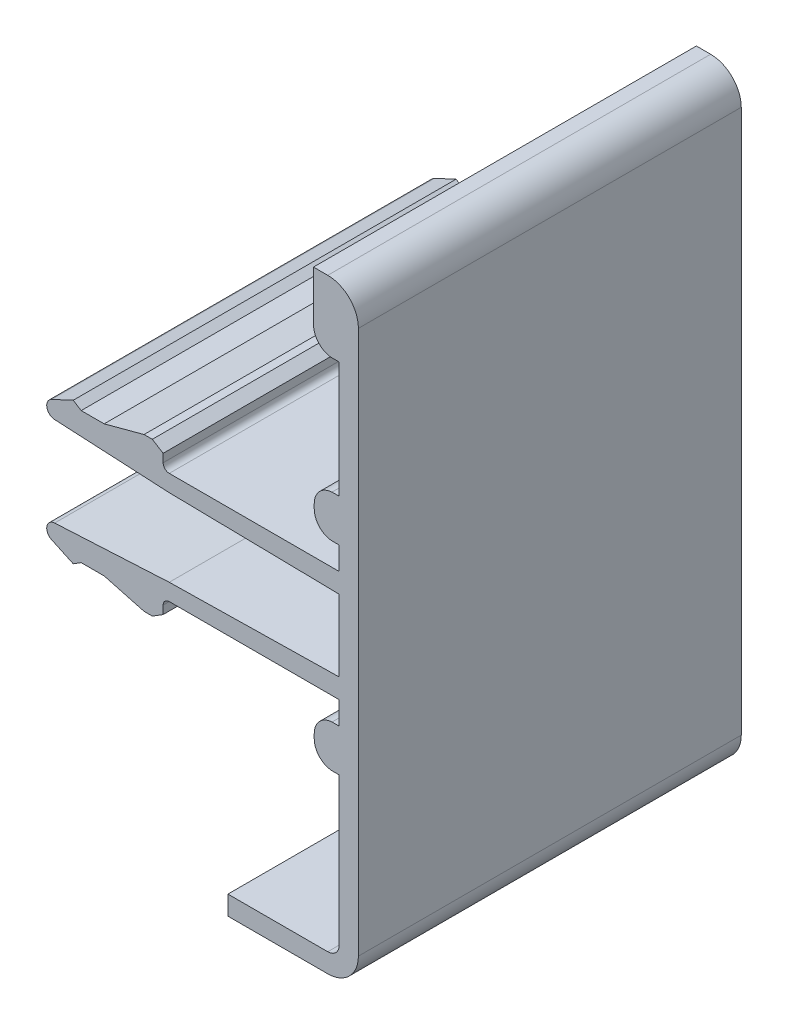
SolidWorks part; units mm, degrees
material "6005-T5"
ref_plane "Front" through (0, 0, 0) normal (0, 0, 1) x (1, 0, 0)
ref_plane "Top" through (0, 0, 0) normal (0, 1, 0) x (1, 0, 0)
ref_plane "Right" through (0, 0, 0) normal (1, 0, 0) x (0, 0, -1)
sketch "Sk Main Extrusion" plane through (0, 0, 0) normal (0, 0, 1) x (1, 0, 0)
  line L0 (-3.83, 2.5328) -> (-11.3125, 2.9251)
  line L5 (-3.83, -2.5328) -> (-11.3125, -2.9251)
  line L6 (6.7989, -5.1201) -> (7.27, -5.1201)
  line L7 (6.7989, -7.8799) -> (7.27, -7.8799)
  line L8 (6.7989, 7.8799) -> (7.27, 7.8799)
  line L9 (6.7989, 5.1201) -> (7.27, 5.1201)
  line L10 (7.27, -7.8799) -> (7.27, -17.5)
  line L11 (6.7981, 15.47) -> (7.27, 15.47)
  line L12 (0, -18.25) -> (0, -19.5)
  line L13 (5.638, 6.65) -> (5.638, 6.35)
  line L14 (7.27, 5.1201) -> (7.27, 3.625)
  line L15 (7.27, 3.625) -> (-3.83, 3.625)
  line L16 (-4.23, 4.025) -> (-4.23, 4.56)
  line L17 (-4.23, 4.56) -> (-4.9341, 5)
  line L18 (-4.9341, 5) -> (-5.4741, 5)
  line L19 (-5.4741, 5) -> (-8.08, 4.3)
  line L20 (-8.08, 4.3) -> (-9.58, 4.3)
  line L21 (-9.58, 4.3) -> (-10.1001, 4.625)
  line L22 (-10.1001, 4.625) -> (-11.5147, 3.9654)
  line L23 (-3.83, 2.5328) -> (7.27, 2.339)
  line L24 (7.27, 2.339) -> (7.27, -2.339)
  line L25 (7.27, -2.339) -> (-3.83, -2.5328)
  line L26 (-11.5147, -3.9654) -> (-10.1001, -4.625)
  line L27 (-10.1001, -4.625) -> (-9.58, -4.3)
  line L28 (-9.58, -4.3) -> (-8.08, -4.3)
  line L29 (-8.08, -4.3) -> (-5.4741, -5)
  line L30 (-5.4741, -5) -> (-4.9341, -5)
  line L31 (-4.9341, -5) -> (-4.23, -4.56)
  line L32 (-4.23, -4.56) -> (-4.23, -4.025)
  line L33 (-3.83, -3.625) -> (7.27, -3.625)
  line L34 (7.27, -3.625) -> (7.27, -5.1201)
  line L35 (5.638, -6.35) -> (5.638, -6.65)
  line L36 (6.52, -18.25) -> (0, -18.25)
  line L37 (0, -19.5) -> (6.52, -19.5)
  line L38 (8.52, -17.5) -> (8.52, 18)
  line L39 (6.52, 20) -> (5.588, 20)
  line L40 (5.588, 20) -> (5.588, 16.75)
  line L41 (7.27, 15.47) -> (7.27, 7.8799)
  arc A0 (6.7989, 7.8799) -> (5.638, 6.65) centre (6.87, 6.65) ccw
  arc A1 (5.638, 6.35) -> (6.7989, 5.1201) centre (6.87, 6.35) ccw
  arc A2 (-4.23, 4.025) -> (-3.83, 3.625) centre (-3.83, 4.025) ccw
  arc A3 (-11.5147, 3.9654) -> (-11.3125, 2.9251) centre (-11.2839, 3.4704) ccw
  arc A4 (-11.3125, -2.9251) -> (-11.5147, -3.9654) centre (-11.2839, -3.4704) ccw
  arc A5 (-3.83, -3.625) -> (-4.23, -4.025) centre (-3.83, -4.025) ccw
  arc A6 (6.7989, -5.1201) -> (5.638, -6.35) centre (6.87, -6.35) ccw
  arc A7 (5.638, -6.65) -> (6.7989, -7.8799) centre (6.87, -6.65) ccw
  arc A8 (6.52, -18.25) -> (7.27, -17.5) centre (6.52, -17.5) ccw
  arc A9 (6.52, -19.5) -> (8.52, -17.5) centre (6.52, -17.5) ccw
  arc A10 (8.52, 18) -> (6.52, 20) centre (6.52, 18) ccw
  arc A11 (5.588, 16.75) -> (6.7981, 15.47) centre (6.87, 16.75) ccw
  point P38 (0, 0)
  point P40 (7.27, 0)
extrude "Main Extrusion" add sketch "Sk Main Extrusion" against normal blind 25
equation "\"Weight kg\"= round ( \"SW-Mass\" , 2 )"
equation "\"Weight lbs\"= round ( \"SW-Mass\" * 2.2046 , 2 )"
equation "\"Length mm\"= round ( \"Length@Main Extrusion\" , 2 )"
equation "\"Length in\"= round ( \"Length@Main Extrusion\" / 25.4 , 3 )"
